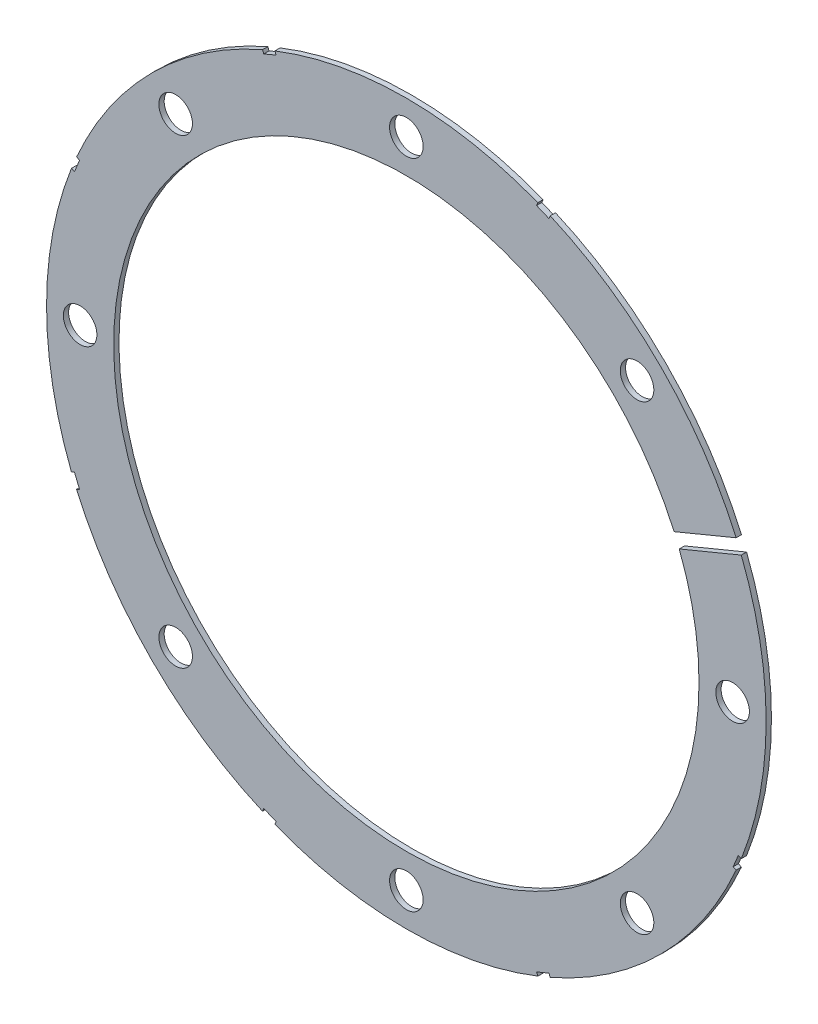
SolidWorks part; units mm, degrees
material "Copper"
ref_plane "Front Plane" through (0, 0, 0) normal (0, 0, 1) x (1, 0, 0)
ref_plane "Top Plane" through (0, 0, 0) normal (0, 1, 0) x (1, 0, 0)
ref_plane "Right Plane" through (0, 0, 0) normal (1, 0, 0) x (0, 0, -1)
sketch "Sketch4" plane through (0, 0, 0) normal (0, 0, 1) x (1, 0, 0)
  circle A0 centre (0, 0) radius 68.072
  dimension "D1" = 136.144
extrude "Boss-Extrude2" add sketch "Sketch4" along normal blind 1
sketch "Sketch5" plane through (0, 0, 1) normal (0, 0, 1) x (1, 0, 0)
  circle A0 centre (0, 0) radius 55.372
  circle A1 centre (0, 0) radius 68.072 construction
  dimension "D2" = 12.7
extrude "Cut-Extrude5" cut sketch "Sketch5" against normal through all
sketch "Sketch6" plane through (0, 0, 1) normal (0, 0, 1) x (1, 0, 0)
  circle A0 centre (61.722, 0) radius 3.175
  circle A4 centre (0, 0) radius 68.072 construction
  dimension "D2" = 6.35
  dimension "D1" = 6.35
extrude "Cut-Extrude6" cut sketch "Sketch6" against normal through all
pattern_circular "CirPattern1" count 8 over 360 about axis through (0, 0, 0) along (0, 0, 1) of "Cut-Extrude6"
sketch "Sketch8" plane through (0, 0, 1) normal (0, 0, 1) x (1, 0, 0)
  line L0 (65.9243, 28.6814) -> (47.1511, 20.9053)
  line L1 (65.9243, 28.6814) -> (66.8963, 26.3347)
  line L2 (47.1511, 20.9053) -> (48.1231, 18.5586)
  line L3 (66.8963, 26.3347) -> (48.1231, 18.5586)
  line L4 (65.9243, 28.6814) -> (48.1231, 18.5586) construction
  line L5 (47.1511, 20.9053) -> (66.8963, 26.3347) construction
  line L6 (0, 0) -> (50.4438, 0) construction
  line L7 (27.4664, 62.991) -> (25.1197, 63.963)
  line L8 (27.4664, 62.991) -> (26.9803, 61.8177)
  line L9 (25.1197, 63.963) -> (24.6337, 62.7897)
  line L10 (26.9803, 61.8177) -> (24.6337, 62.7897)
  line L11 (25.1197, 63.963) -> (26.9803, 61.8177) construction
  line L12 (27.4664, 62.991) -> (24.6337, 62.7897) construction
  line L13 (-25.1197, 63.963) -> (-27.4664, 62.991)
  line L14 (-25.1197, 63.963) -> (-24.6337, 62.7897)
  line L15 (-24.6337, 62.7897) -> (-26.9803, 61.8177)
  line L16 (-27.4664, 62.991) -> (-26.9803, 61.8177)
  line L17 (-25.1197, 63.963) -> (-26.9803, 61.8177) construction
  line L18 (-27.4664, 62.991) -> (-24.6337, 62.7897) construction
  line L19 (-62.991, 27.4664) -> (-63.963, 25.1197)
  line L20 (-62.991, 27.4664) -> (-61.8177, 26.9803)
  line L21 (-61.8177, 26.9803) -> (-62.7897, 24.6337)
  line L22 (-63.963, 25.1197) -> (-62.7897, 24.6337)
  line L23 (-62.991, 27.4664) -> (-62.7897, 24.6337) construction
  line L24 (-63.963, 25.1197) -> (-61.8177, 26.9803) construction
  line L25 (-63.963, -25.1197) -> (-62.991, -27.4664)
  line L26 (-63.963, -25.1197) -> (-62.7897, -24.6337)
  line L27 (-62.7897, -24.6337) -> (-61.8177, -26.9803)
  line L28 (-62.991, -27.4664) -> (-61.8177, -26.9803)
  line L29 (-63.963, -25.1197) -> (-61.8177, -26.9803) construction
  line L30 (-62.991, -27.4664) -> (-62.7897, -24.6337) construction
  line L31 (-27.4664, -62.991) -> (-25.1197, -63.963)
  line L32 (-27.4664, -62.991) -> (-26.9803, -61.8177)
  line L33 (-26.9803, -61.8177) -> (-24.6337, -62.7897)
  line L34 (-25.1197, -63.963) -> (-24.6337, -62.7897)
  line L35 (-27.4664, -62.991) -> (-24.6337, -62.7897) construction
  line L36 (-25.1197, -63.963) -> (-26.9803, -61.8177) construction
  line L37 (25.1197, -63.963) -> (27.4664, -62.991)
  line L38 (25.1197, -63.963) -> (24.6337, -62.7897)
  line L39 (24.6337, -62.7897) -> (26.9803, -61.8177)
  line L40 (27.4664, -62.991) -> (26.9803, -61.8177)
  line L41 (25.1197, -63.963) -> (26.9803, -61.8177) construction
  line L42 (27.4664, -62.991) -> (24.6337, -62.7897) construction
  line L43 (62.991, -27.4664) -> (63.963, -25.1197)
  line L44 (62.991, -27.4664) -> (61.8177, -26.9803)
  line L45 (61.8177, -26.9803) -> (62.7897, -24.6337)
  line L46 (63.963, -25.1197) -> (62.7897, -24.6337)
  line L47 (62.991, -27.4664) -> (62.7897, -24.6337) construction
  line L48 (63.963, -25.1197) -> (61.8177, -26.9803) construction
  circle A0 centre (0, 0) radius 68.072 construction
  point P1 (57.0237, 23.62)
  point P3 (26.05, 62.8903)
  point P11 (-26.05, 62.8903)
  point P20 (-62.8903, 26.05)
  point P25 (-62.8903, -26.05)
  point P26 (0, 0)
  point P31 (-26.05, -62.8903)
  point P36 (26.05, -62.8903)
  point P41 (62.8903, -26.05)
  point P46 (0, 0)
  dimension "D1" = 20.32
  dimension "D2" = 6.35
  dimension "D3" = 2.54
  dimension "D4" = 22.5
  dimension "D5" = 1.27
  dimension "D6" = 2.54
  dimension "D7" = 1.27
  dimension "D8" = 1.27
  dimension "D9" = 0.635
  dimension "D10" = 67.5
  dimension "D12" = 0.635
  dimension "D13" = 0.635
  dimension "D11" = 7
extrude "Cut-Extrude11" cut sketch "Sketch8" against normal through all
